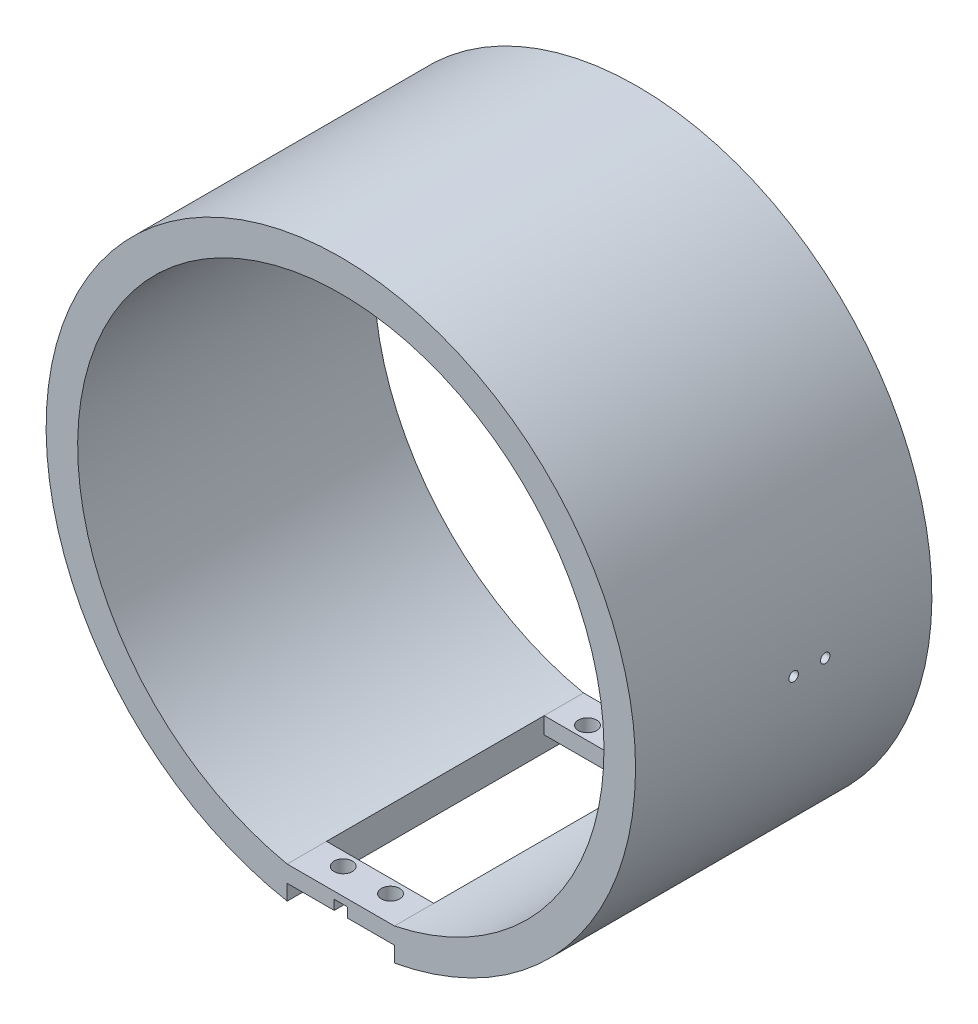
SolidWorks part; units mm, degrees
ref_plane "Front Plane" through (0, 0, 0) normal (0, 0, 1) x (1, 0, 0)
ref_plane "Top Plane" through (0, 0, 0) normal (0, 1, 0) x (1, 0, 0)
ref_plane "Right Plane" through (0, 0, 0) normal (1, 0, 0) x (0, 0, -1)
sketch "Sketch1" plane through (0, 0, 0) normal (0, 0, 1) x (1, 0, 0)
  circle A0 centre (0, 0) radius 93.4029
  circle A1 centre (0, 0) radius 83.4029
  dimension "D1" = 10
extrude "Boss-Extrude1" add sketch "Sketch1" against normal offset from surface (93.92 mm away) 6
ref_plane "Plane1" through (0, 0, -46.96) normal (0, 0, 1) x (1, 0, 0)
ref_plane "Plane2" through (0, -93.4029, 0) normal (0, -1, 0) x (-1, 0, 0)
sketch "Sketch7" plane through (0, 0, 0) normal (0, 0, 1) x (1, 0, 0)
  line L0 (15, -75.43) -> (15, -80.83) construction
  line L1 (-15, -75.43) -> (-15, -80.83) construction
  line L2 (15, -75.43) -> (15, -80.83) construction
  line L3 (-15, -75.43) -> (-15, -80.83) construction
  line L4 (-17, -81.652) -> (17, -81.652)
  line L5 (-15, -75.43) -> (15, -75.43) construction
  line L6 (0, -75.43) -> (0, -81.652) construction
  circle A0 centre (0, 0) radius 83.4029 construction
  arc A1 (-17, -81.652) -> (17, -81.652) centre (0, 0) ccw
  point P10 (0, 0)
  point P11 (-0.1794, -81.7074)
  point P12 (0.312, -81.8669)
  dimension "D1" = 2
extrude "Boss-Extrude3" add sketch "Sketch7" against normal up to surface (93.92 mm away) contours L4 A1 up to face at (0, -93.4029, -93.92)
sketch "Sketch2" plane through (0, -93.4029, 0) normal (0, -1, 0) x (-1, 0, 0)
  line L4 (-15, 79.46) -> (15, 79.46) construction
  line L7 (1.095, 14.46) -> (15, 14.46) construction
  line L13 (-15, 79.46) -> (15, 79.46) construction
  line L14 (1.095, 14.46) -> (15, 14.46) construction
  line L15 (17, 81.46) -> (-17, 81.46)
  line L16 (15, 14.46) -> (-15, 14.46)
  line L17 (15, 14.46) -> (15, 79.46)
  line L18 (15, 79.46) -> (-15, 79.46)
  line L19 (-15, 14.46) -> (-15, 79.46)
  line L20 (-17, 12.46) -> (-17, 81.46)
  line L21 (17, 12.46) -> (-17, 12.46)
  line L22 (17, 12.46) -> (17, 81.46)
  dimension "D1" = 2
extrude "Cut-Extrude1" cut sketch "Sketch2" against normal up to next contours L20 L15 L22 L21
sketch "Sketch3" plane through (0, -93.4029, 0) normal (0, -1, 0) x (-1, 0, 0)
  line L0 (93.4029, 93.92) -> (-93.4029, 93.92) construction
  line L1 (-17, 81.46) -> (17, 81.46)
  line L2 (-17, 81.46) -> (-17, 93.92)
  line L3 (-17, 93.92) -> (17, 93.92)
  line L4 (17, 81.46) -> (17, 93.92)
  line L5 (-17, 81.46) -> (-17, 12.46) construction
  line L6 (-17, 12.46) -> (17, 12.46)
  line L7 (-17, 12.46) -> (-17, 0)
  line L8 (-17, 0) -> (17, 0)
  line L9 (17, 12.46) -> (17, 0)
  line L10 (17, 81.46) -> (17, 12.46) construction
extrude "Cut-Extrude2" cut sketch "Sketch3" against normal up to surface (6.4729 mm away)
sketch "Sketch4" plane through (0, -86.93, 0) normal (0, -1, 0) x (1, 0, 0)
  arc A0 (8.9, -87.92) -> (6.1, -87.92) centre (7.5, -85.67) ccw construction
  arc A1 (-6.1, -87.92) -> (-8.9, -87.92) centre (-7.5, -85.67) ccw construction
  arc A2 (6.1, -6) -> (8.9, -6) centre (7.5, -8.25) ccw construction
  arc A3 (-8.9, -6) -> (-6.1, -6) centre (-7.5, -8.25) ccw construction
  arc A4 (8.9, -87.92) -> (6.1, -87.92) centre (7.5, -85.67) ccw
  arc A5 (-6.1, -87.92) -> (-8.9, -87.92) centre (-7.5, -85.67) ccw
  arc A6 (6.1, -6) -> (8.9, -6) centre (7.5, -8.25) ccw
  arc A7 (-8.9, -6) -> (-6.1, -6) centre (-7.5, -8.25) ccw
hole_wizard "M5 Clearance Hole1" positions "3DSketch1" profile "Sketch6" hole size "M5" standard "ANSI Metric"
sketch3d "3DSketch1"
  point P0 (-7.5, -86.93, -8.25)
  point P3 (7.5, -86.93, -8.25)
  point P6 (-7.5, -86.93, -85.67)
  point P9 (7.5, -86.93, -85.67)
sketch "Sketch6" plane through (-7.5, -86.93, -8.25) normal (1, 0, 0) x (0, 0, -1)
  line L0 (0, 0) -> (0, 172.0764)
  line L1 (0, 172.0764) -> (2.9, 170.3339)
  line L2 (2.9, 170.3339) -> (2.9, 0)
  line L5 (2.9, 0) -> (0, 0)
  line L10 (0, 172.0764) -> (-2.9, 170.3339) construction
  line L11 (0, -6.35) -> (0, 107.95) construction
  dimension "Hole Dia." = 5.8
  dimension "Hole Depth" = 170.3339
  dimension "Drill Angle" = 118
sketch "Sketch8" plane through (0, 0, 0) normal (0, 0, 1) x (1, 0, 0)
  line L0 (-17, -86.93) -> (17, -86.93) construction
  line L1 (-2.095, -86.93) -> (2.095, -86.93)
  line L2 (-2.095, -86.93) -> (-2.095, -83.86)
  line L3 (-2.095, -83.86) -> (2.095, -83.86)
  line L4 (2.095, -86.93) -> (2.095, -83.86)
  line L5 (1.095, -86.93) -> (-1.095, -86.93) construction
  line L6 (1.095, -86.93) -> (-1.095, -86.93)
  line L7 (1.095, -84.86) -> (1.095, -86.93) construction
  line L8 (1.095, -84.86) -> (1.095, -86.93) construction
  point P6 (0, -86.93)
  point P7 (0, -86.93)
  dimension "D1" = 1
  dimension "D2" = 1
extrude "Cut-Extrude3" cut sketch "Sketch8" against normal up to surface (12.46 mm away) contours L2 L3 L4 L1 up to face at (0, -84.291, -12.46)
ref_plane "Plane3" through (93.4029, 0, 0) normal (1, 0, 0) x (0, 0, -1)
sketch "Sketch9" plane through (93.4029, 0, 0) normal (1, 0, 0) x (0, 0, -1)
  point P0 (50.1169, 0)
  point P1 (0, 0)
  point P3 (60.1169, 0)
  point P5 (0, 0)
hole_wizard "M6 Clearance Hole1" positions "3DSketch2" profile "Sketch10" hole size "M6" standard "ANSI Metric"
sketch3d "3DSketch2"
  point P0 (93.4029, 0, -60.1169)
  point P2 (93.4029, 0, -50.1169)
  point P5 (0, 0, 0)
  point P6 (93.2283, 5.7088, -48.1474)
  point P10 (0, 0, 0)
  point P12 (0, 0, 0)
sketch "Sketch10" plane through (93.4029, 0, -60.1169) normal (0, 1, 0) x (0, 0, -1)
  line L0 (0, 0) -> (0, 10)
  line L1 (0, 10) -> (1.5, 10)
  line L2 (1.5, 10) -> (1.5, 0)
  line L5 (1.5, 0) -> (0, 0)
  line L11 (0, -6.35) -> (0, 107.95) construction
  dimension "Thru Hole Dia." = 3
  dimension "Thru Hole Depth" = 10
